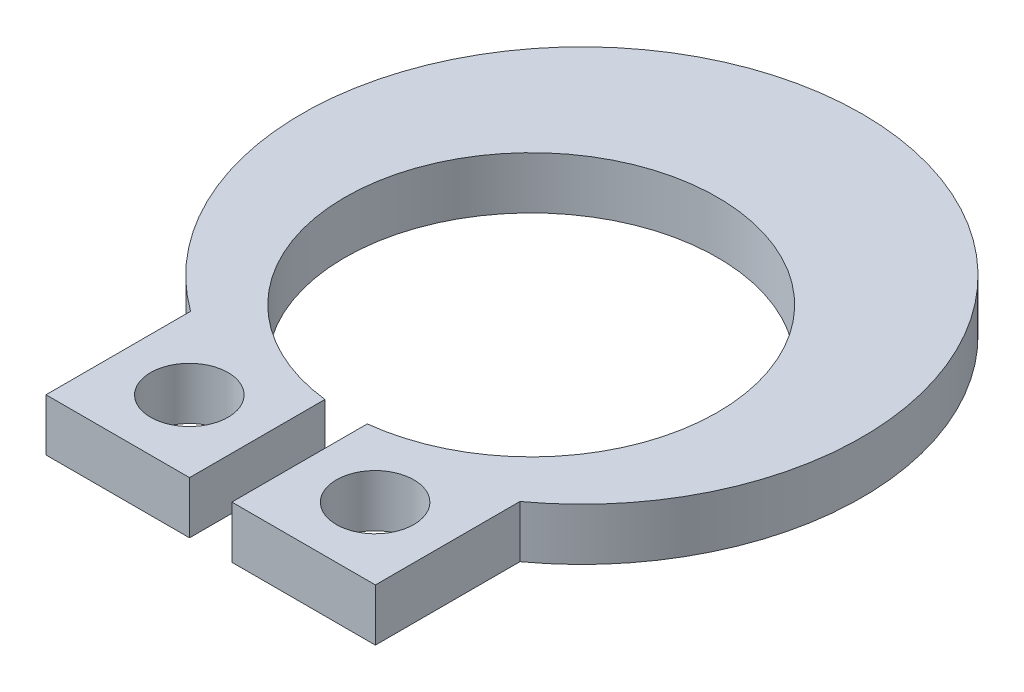
SolidWorks part; units mm, degrees
ref_plane "Front Plane" through (0, 0, 0) normal (0, 0, 1) x (1, 0, 0)
ref_plane "Top Plane" through (0, 0, 0) normal (0, 1, 0) x (1, 0, 0)
ref_plane "Right Plane" through (0, 0, 0) normal (1, 0, 0) x (0, 0, -1)
sketch "Sketch4" plane through (0, 0, 0) normal (0, 1, 0) x (1, 0, 0)
  line L0 (-2.8067, -5.4621) -> (-0.3607, -5.4621)
  line L1 (-2.8067, -2.9983) -> (-2.8067, -5.4621)
  line L2 (2.8067, -2.9983) -> (2.8067, -5.4621)
  line L3 (0, -7.9097) -> (0, 7.1432) construction
  line L4 (-5.9014, 0) -> (6.1037, 0) construction
  line L5 (0.3607, -5.4621) -> (0.3607, -3.1544)
  line L6 (-0.3607, -5.4621) -> (-0.3607, -3.1544)
  line L7 (0.3607, -5.4621) -> (2.8067, -5.4621)
  line L8 (-0.3607, -7.9097) -> (-0.3607, 7.1432) construction
  line L9 (0.3607, -7.9097) -> (0.3607, 7.1432) construction
  arc A0 (0.3607, -3.1544) -> (-0.3607, -3.1544) centre (0, 0) ccw
  arc A1 (2.8067, -2.9983) -> (-2.8067, -2.9983) centre (0, 0.8636) ccw
  dimension "D1" = 11.0998
  dimension "D5" = 3.175
  dimension "D6" = 0.8636
  dimension "D2" = 2.4638
  dimension "D7" = 5.6134
  dimension "D3" = 0.3607
  dimension "D4" = 0.3607
extrude "Extrude1" add sketch "Sketch4" along normal blind 0.889
sketch "Sketch5" plane through (0, 0, 0) normal (0, 1, 0) x (1, 0, 0)
  line L0 (1.5829, -5.4855) -> (1.5829, -1.2171) construction
  line L1 (2.8052, -4.2536) -> (0.3607, -4.2432) construction
  circle A0 centre (1.5829, -4.2432) radius 0.6604
  dimension "D1" = 1.3208
extrude "Cut-Extrude1" cut sketch "Sketch5" along normal through all
mirror "Mirror1" about plane through (0, 0, 0) normal (1, 0, 0) of "Cut-Extrude1"
